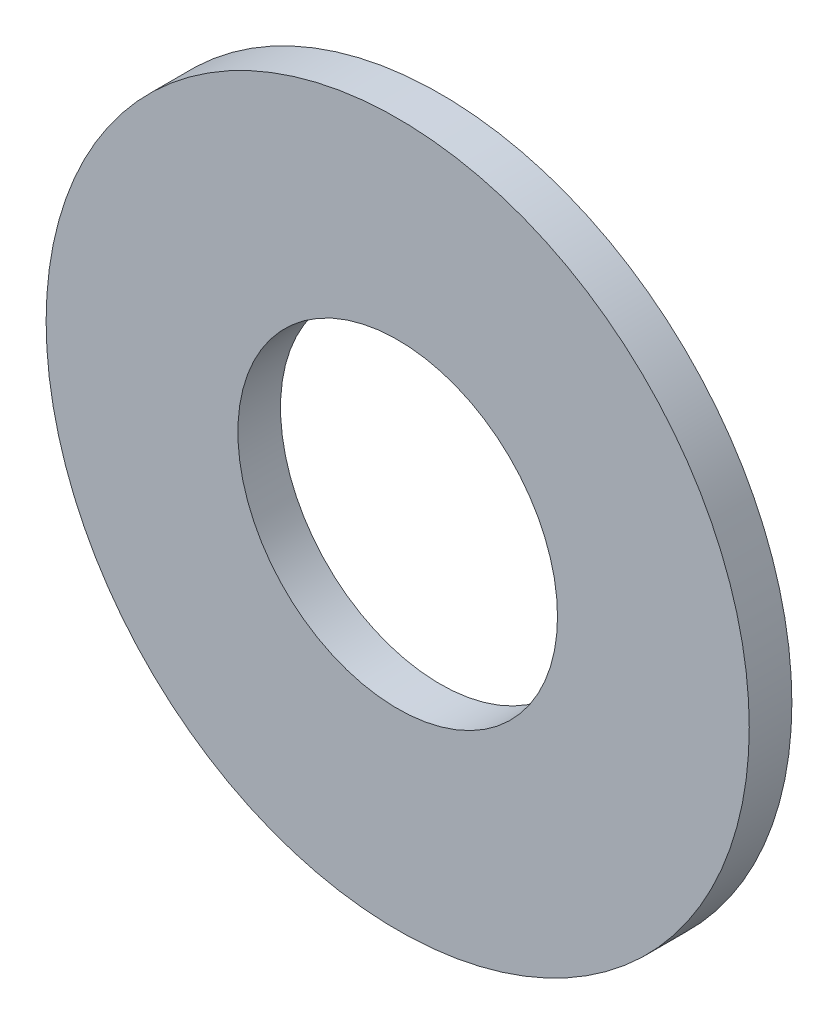
SolidWorks part; units mm, degrees
ref_plane "Front Plane" through (0, 0, 0) normal (0, 0, 1) x (1, 0, 0)
ref_plane "Top Plane" through (0, 0, 0) normal (0, 1, 0) x (1, 0, 0)
ref_plane "Right Plane" through (0, 0, 0) normal (1, 0, 0) x (0, 0, -1)
sketch "Sketch1" plane through (0, 0, 0) normal (0, 0, 1) x (1, 0, 0)
  circle A0 centre (0, 0) radius 82.5
  circle A1 centre (0, 0) radius 37.5
  dimension "D1" = 165
  dimension "D2" = 75
extrude "Boss-Extrude1" add sketch "Sketch1" along normal blind 10
